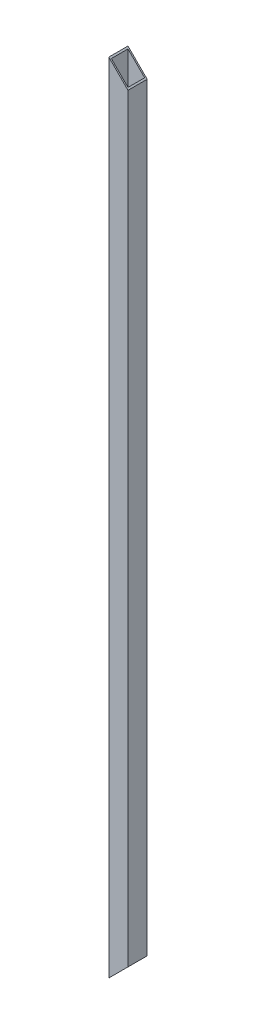
SolidWorks part; units mm, degrees
material "Aleación 1060"
ref_plane "Alzado" through (0, 0, 0) normal (0, 0, 1) x (1, 0, 0)
ref_plane "Planta" through (0, 0, 0) normal (0, 1, 0) x (1, 0, 0)
ref_plane "Vista lateral" through (0, 0, 0) normal (1, 0, 0) x (0, 0, -1)
ref_plane "Plano1" through (0, 0, 19) normal (0, 0, 1) x (1, 0, 0)
sketch "Croquis1" plane through (0, 0, 19) normal (0, 0, 1) x (1, 0, 0)
  line L0 (19, 1542) -> (-19, 1580)
  line L1 (-19, 1580) -> (-19, 0)
  line L2 (-19, 0) -> (19, 38)
  line L3 (19, 38) -> (19, 1542)
extrude "Saliente-Extruir1" add sketch "Croquis1" against normal blind 2.5
sketch "Croquis2" plane through (0, 0, 16.5) normal (0, 0, -1) x (-1, 0, 0)
  line L0 (-16.5, 1544.5) -> (-16.5, 35.5)
  line L1 (-16.5, 35.5) -> (-19, 38)
  line L2 (-19, 38) -> (-19, 1542)
  line L3 (-19, 1542) -> (-16.5, 1544.5)
extrude "Saliente-Extruir2" add sketch "Croquis2" along normal blind 33
sketch "Croquis3" plane through (0, 0, 16.5) normal (0, 0, -1) x (-1, 0, 0)
  line L0 (16.5, 2.5) -> (16.5, 1577.5)
  line L1 (16.5, 1577.5) -> (19, 1580)
  line L2 (19, 1580) -> (19, 0)
  line L3 (19, 0) -> (16.5, 2.5)
extrude "Saliente-Extruir3" add sketch "Croquis3" along normal blind 33
sketch "Croquis4" plane through (0, 0, -16.5) normal (0, 0, -1) x (-1, 0, 0)
  line L0 (-19, 1542) -> (19, 1580)
  line L1 (19, 1580) -> (19, 0)
  line L2 (19, 0) -> (-19, 38)
  line L3 (-19, 38) -> (-19, 1542)
extrude "Saliente-Extruir4" add sketch "Croquis4" along normal blind 2.5
